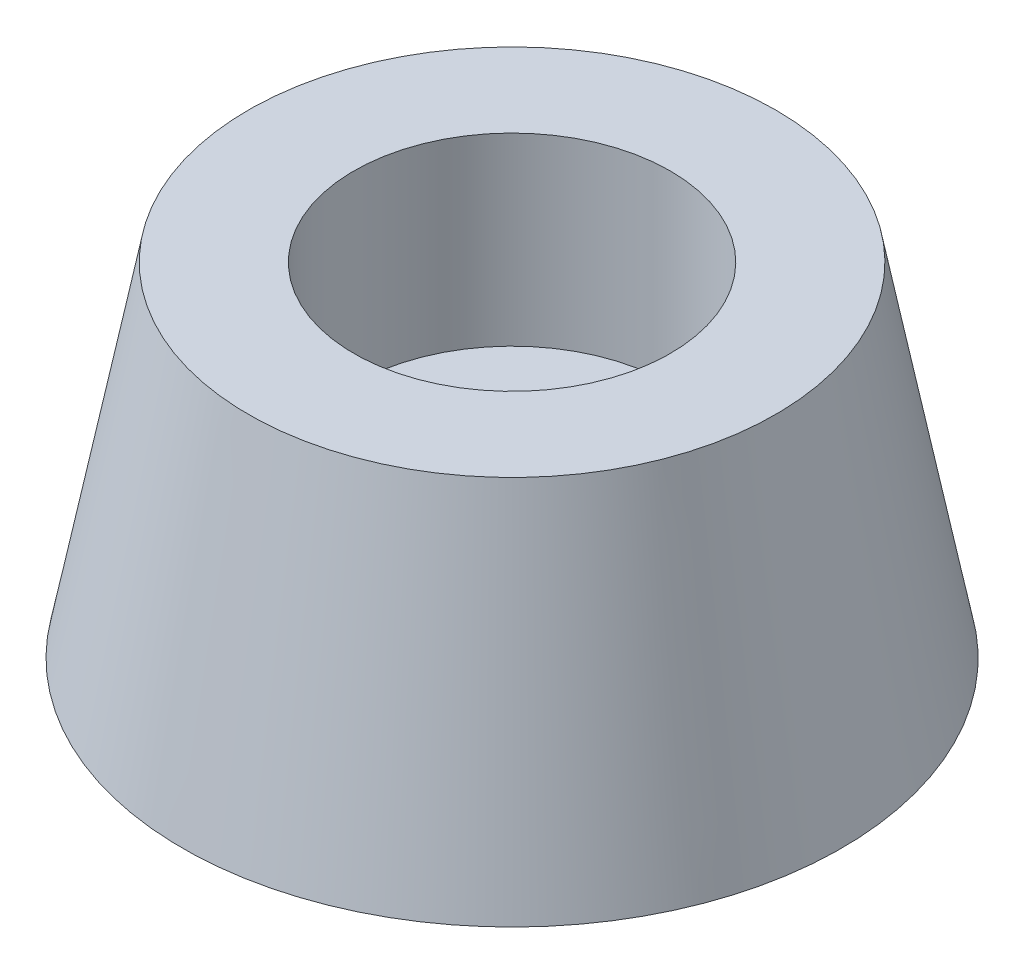
SolidWorks part; units mm, degrees
ref_plane "前视基准面" through (0, 0, 0) normal (0, 0, 1) x (1, 0, 0)
ref_plane "上视基准面" through (0, 0, 0) normal (0, 1, 0) x (1, 0, 0)
ref_plane "右视基准面" through (0, 0, 0) normal (1, 0, 0) x (0, 0, -1)
sketch "草图1" plane through (0, 0, 0) normal (0, 0, 1) x (1, 0, 0)
  line L0 (0, 0) -> (0, 12834.0169) construction
  line L1 (-3, 0) -> (-12.5, 0)
  line L2 (-12.5, 0) -> (-10, 13)
  line L3 (-10, 13) -> (-6, 13)
  line L4 (-6, 13) -> (-6, 6)
  line L5 (-6, 6) -> (-3, 6)
  line L6 (-3, 6) -> (-3, 0)
  dimension "D1" = 25
  dimension "D2" = 6
  dimension "D3" = 13
  dimension "D4" = 12
  dimension "D5" = 20
  dimension "D6" = 6
revolve "旋转1" add sketch "草图1" angle 360 about L0
